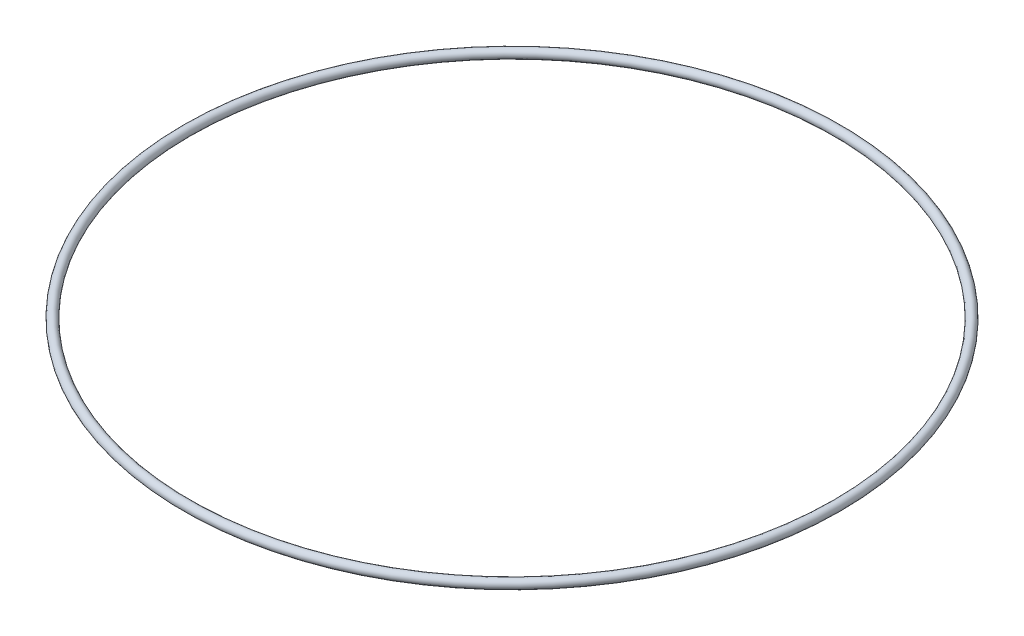
SolidWorks part; units mm, degrees
material "Rubber"
ref_plane "Front Plane" through (0, 0, 0) normal (0, 0, 1) x (1, 0, 0)
ref_plane "Top Plane" through (0, 0, 0) normal (0, 1, 0) x (1, 0, 0)
ref_plane "Right Plane" through (0, 0, 0) normal (1, 0, 0) x (0, 0, -1)
sketch "Sketch1" plane through (0, 0, 0) normal (0, 0, 1) x (1, 0, 0)
  line L0 (0, -29.0616) -> (0, 35.4116) construction
  circle A1 centre (56.515, 3.175) radius 0.7937
  dimension "D2" = 1.5875
  dimension "D1" = 56.515
revolve "Revolve1" add sketch "Sketch1" angle 360 about L0
